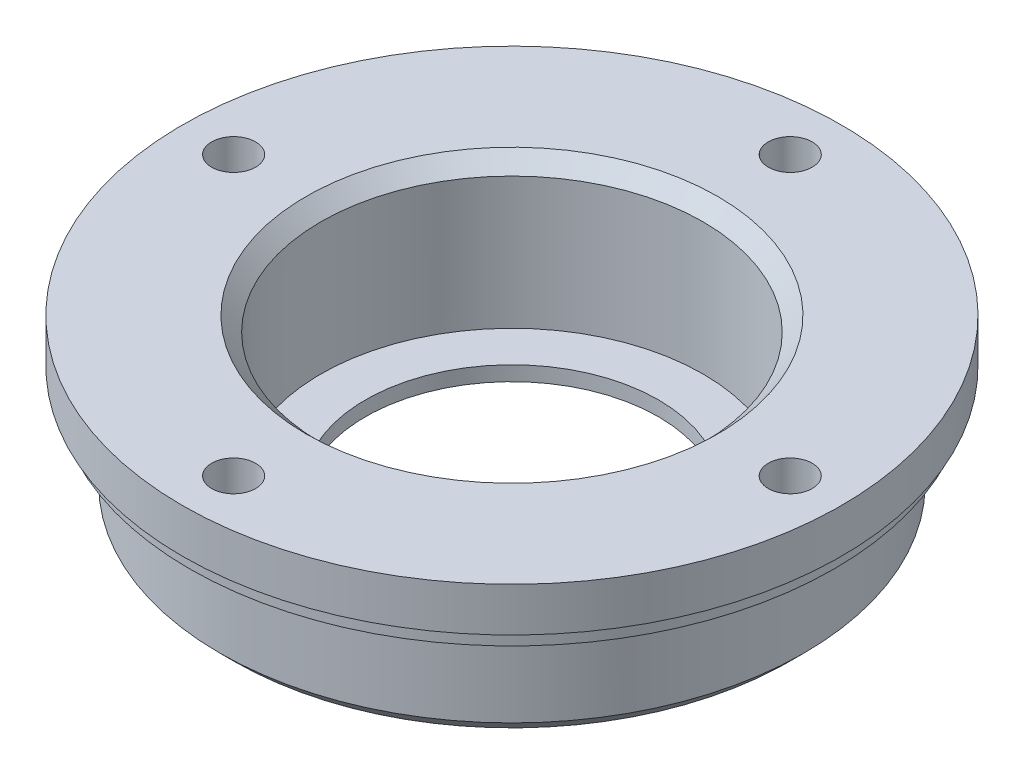
SolidWorks part; units mm, degrees
ref_plane "Front Plane" through (0, 0, 0) normal (0, 0, 1) x (1, 0, 0)
ref_plane "Top Plane" through (0, 0, 0) normal (0, 1, 0) x (1, 0, 0)
ref_plane "Right Plane" through (0, 0, 0) normal (1, 0, 0) x (0, 0, -1)
sketch "Sketch1" plane through (0, 0, 0) normal (0, 1, 0) x (1, 0, 0)
  circle A0 centre (0, 0) radius 19.95
  circle A1 centre (0, 0) radius 13.05
  dimension "D1" = 39.9
  dimension "D2" = 26.1
extrude "Boss-Extrude1" add sketch "Sketch1" along normal blind 7
sketch "Sketch2" plane through (0, 0, 0) normal (0, -1, 0) x (-1, 0, 0)
  circle A0 centre (0, 0) radius 10
  circle A1 centre (0, 0) radius 13.05 construction
  circle A2 centre (0, 0) radius 13.05
  dimension "D1" = 20
extrude "Boss-Extrude2" add sketch "Sketch2" against normal blind 1
sketch "Sketch3" plane through (0, 7, 0) normal (0, 1, 0) x (1, 0, 0)
  circle A0 centre (0, 0) radius 13.05 construction
  circle A1 centre (0, 0) radius 13.05
  circle A2 centre (0, 0) radius 22
  dimension "D1" = 44
extrude "Boss-Extrude3" add sketch "Sketch3" along normal blind 1
sketch "Sketch4" plane through (0, 8, 0) normal (0, 1, 0) x (1, 0, 0)
  circle A0 centre (0, 0) radius 22.5
  circle A1 centre (0, 19) radius 1.5
  circle A2 centre (19, 0) radius 1.5
  circle A3 centre (0, -19) radius 1.5
  circle A4 centre (-19, 0) radius 1.5
  circle A5 centre (0, 0) radius 13.05 construction
  circle A6 centre (0, 0) radius 13.05
  point P14 (0, 0)
  dimension "D2" = 3
  dimension "D3" = 45
  dimension "D1" = 19
  dimension "D4" = 4
extrude "Boss-Extrude7" add sketch "Sketch4" along normal blind 3
chamfer "Chamfer1" distance 1 angle 45 2 edges at (0, 0, 19.95) (0, 11, 13.05)
sketch "Sketch6" plane through (0, 8, 0) normal (0, 1, 0) x (1, 0, 0)
  circle A0 centre (-19, 0) radius 1.5 construction
  circle A1 centre (0, -19) radius 1.5 construction
  circle A2 centre (19, 0) radius 1.5 construction
  circle A3 centre (0, 19) radius 1.5 construction
  circle A4 centre (-19, 0) radius 1.5
  circle A5 centre (0, -19) radius 1.5
  circle A6 centre (19, 0) radius 1.5
  circle A7 centre (0, 19) radius 1.5
extrude "Cut-Extrude1" cut sketch "Sketch6" against normal blind 1
